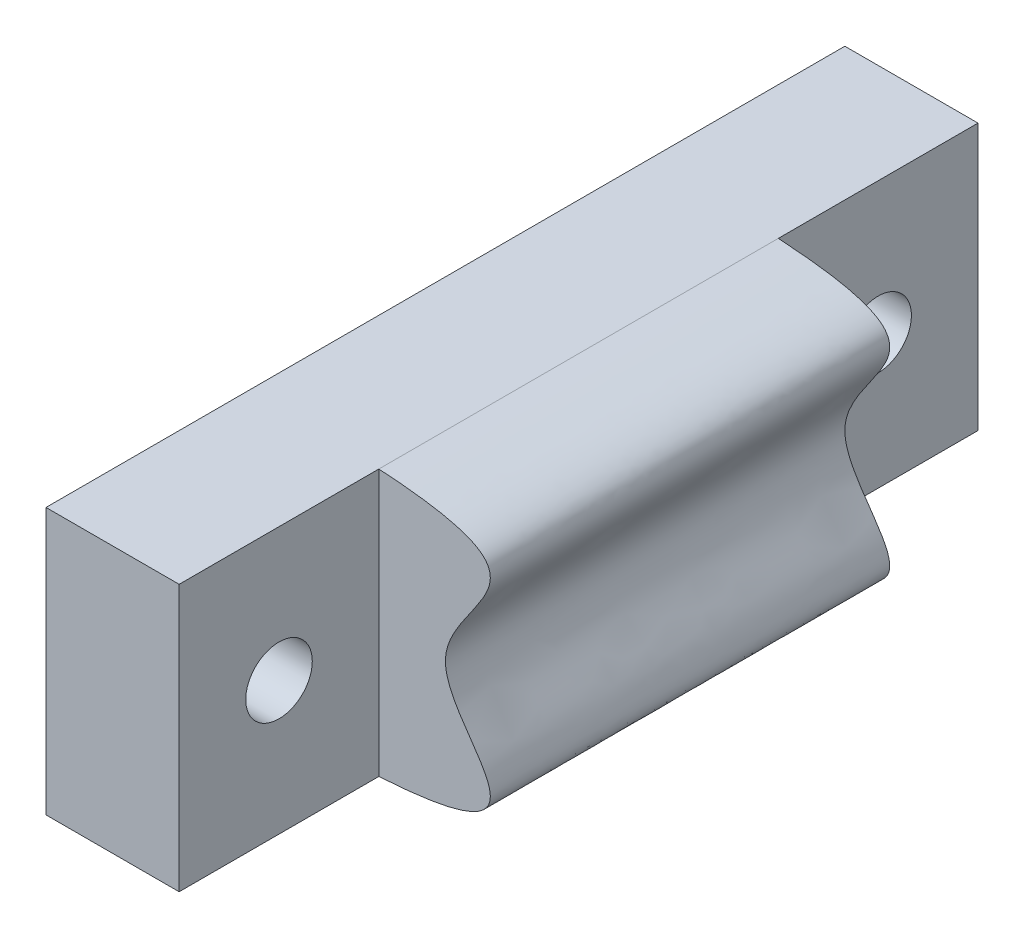
SolidWorks part; units mm, degrees
ref_plane "Front Plane" through (0, 0, 0) normal (0, 0, 1) x (1, 0, 0)
ref_plane "Top Plane" through (0, 0, 0) normal (0, 1, 0) x (1, 0, 0)
ref_plane "Right Plane" through (0, 0, 0) normal (1, 0, 0) x (0, 0, -1)
sketch "Sketch1" plane through (0, 0, 0) normal (0, 0, 1) x (1, 0, 0)
  line L0 (6.35, 0) -> (12.7, 0) construction
  line L1 (-6.35, -12.7) -> (6.35, -12.7)
  line L2 (-6.35, -12.7) -> (-6.35, 12.7)
  line L3 (-6.35, 12.7) -> (6.35, 12.7)
  line L5 (-6.35, -12.7) -> (6.35, 12.7) construction
  line L6 (-6.35, 12.7) -> (6.35, -12.7) construction
  line L9 (6.35, 6.35) -> (15.875, 6.35) construction
  line L10 (6.35, -6.35) -> (15.875, -6.35) construction
  spline S0 degree 3 poles (6.35, 12.7) (25.7153, 11.5045) (-0.3153, 0) (25.7153, -11.5045) (6.35, -12.7) knots 0 0 0 0 0.5 1 1 1 1
  point P0 (0, 0)
  point P11 (6.35, 12.7)
  dimension "D1" = 12.7
  dimension "D2" = 25.4
  dimension "D3" = 25.4
  dimension "D5" = 9.525
extrude "Boss-Extrude1" add sketch "Sketch1" along normal blind 76.2
sketch "Sketch2" plane through (0, 0, 76.2) normal (0, 0, 1) x (1, 0, 0)
  line L0 (6.35, 12.7) -> (6.35, -12.7)
  spline S0 degree 3 poles (-4965.6317, 513.4453) (350.0483, -58.5707) (-324.6462, -0.0002) (350.0441, 58.5703) (-4965.5341, -513.4348) knots -2.045558 -2.045558 -2.045558 -2.045558 0.5 3.045542 3.045542 3.045542 3.045542 only from (6.35, -12.7) to (6.35, 12.7) construction
  spline S1 degree 3 poles (6.35, -12.7) (25.7153, -11.5045) (-0.3153, 0) (25.7153, 11.5045) (6.35, 12.7) knots 0 0 0 0 0.5 1 1 1 1
extrude "Cut-Extrude1" cut sketch "Sketch2" against normal blind 19.05
sketch "Sketch3" plane through (0, 0, 0) normal (0, 0, -1) x (-1, 0, 0)
  line L0 (-6.35, 12.7) -> (-6.35, -12.7)
  spline S0 degree 3 poles (1983.0798, 191.8673) (-204.6811, -44.1845) (179.2796, -0.0002) (-204.6781, 44.1842) (1983.0287, -191.8618) knots -1.420317 -1.420317 -1.420317 -1.420317 0.5 2.420302 2.420302 2.420302 2.420302 only from (-6.35, -12.7) to (-6.35, 12.7) construction
  spline S1 degree 3 poles (-6.35, -12.7) (-25.7153, -11.5045) (0.3153, 0) (-25.7153, 11.5045) (-6.35, 12.7) knots 0 0 0 0 0.5 1 1 1 1
extrude "Cut-Extrude2" cut sketch "Sketch3" against normal blind 19.05
sketch "Sketch4" plane through (6.35, 0, 0) normal (1, 0, 0) x (0, 0, -1)
  line L0 (-76.2, 0) -> (0, 0) construction
  line L1 (-76.2, 12.7) -> (-76.2, -12.7) construction
  line L2 (-66.675, 12.7) -> (-66.675, -12.7) construction
  line L3 (-76.2, 12.7) -> (-57.15, 12.7) construction
  line L4 (-76.2, -12.7) -> (-57.15, -12.7) construction
  line L5 (-9.525, 12.7) -> (-9.525, -12.7) construction
  line L6 (-19.05, 12.7) -> (0, 12.7) construction
  line L7 (-19.05, -12.7) -> (0, -12.7) construction
  circle A0 centre (-66.675, 0) radius 3.175
  circle A1 centre (-9.525, 0) radius 3.175
  dimension "D1" = 6.35
  dimension "D2" = 6.35
extrude "Cut-Extrude3" cut sketch "Sketch4" against normal through all
